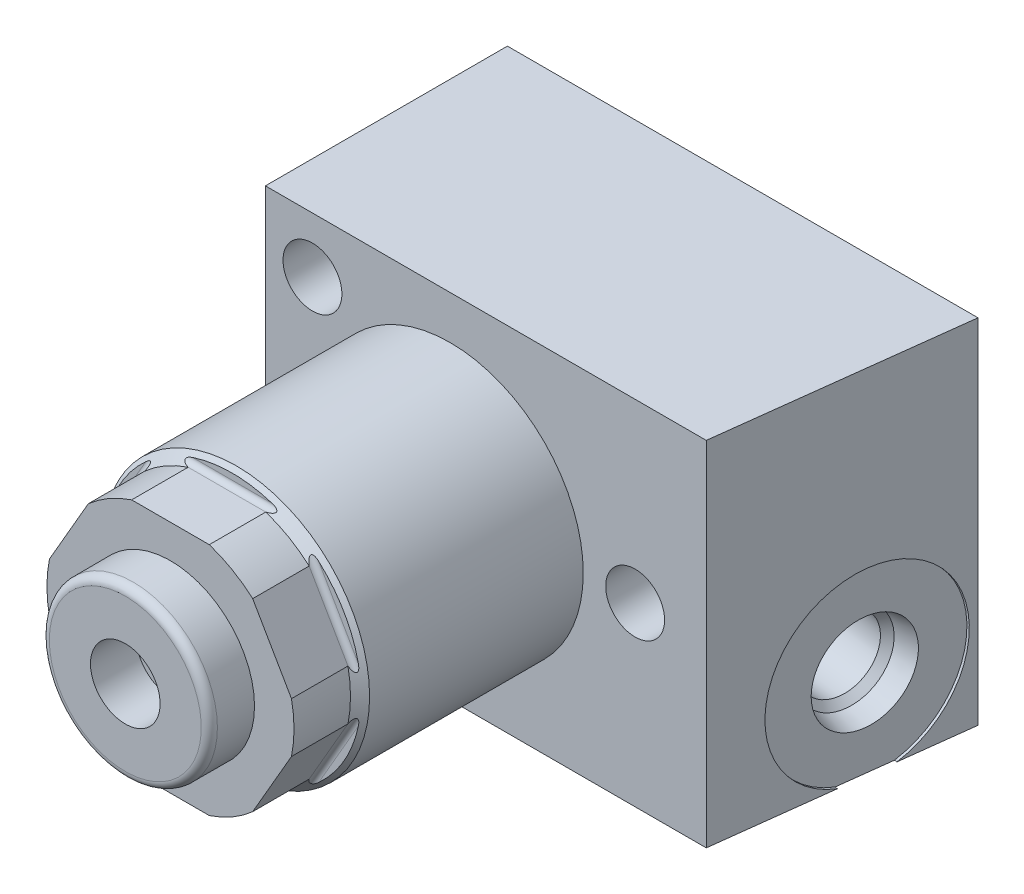
SolidWorks part; units mm, degrees
material "Alloy Steel"
ref_plane "Front Plane" through (0, 0, 0) normal (0, 0, 1) x (1, 0, 0)
ref_plane "Top Plane" through (0, 0, 0) normal (0, 1, 0) x (1, 0, 0)
ref_plane "Right Plane" through (0, 0, 0) normal (1, 0, 0) x (0, 0, -1)
ref_plane "Plane1" through (0, 0, 0) normal (0, 0, 1) x (1, 0, 0)
sketch "Sketch1" plane through (0, 0, 0) normal (0, 0, 1) x (1, 0, 0)
  circle A0 centre (0, 0) radius 12.573
  dimension "D1" = 25.146
extrude "Extrude1" add sketch "Sketch1" along normal blind 40.005
ref_plane "Plane2" through (0, 0, 0) normal (1, 0, 0) x (0, 0, 1)
sketch "Sketch2" plane through (0, 0, 0) normal (1, 0, 0) x (0, 0, 1)
  line L0 (34.163, 12.573) -> (34.163, 11.5887)
  line L1 (34.671, 11.0808) -> (40.005, 11.0808)
  line L2 (33.8709, 0) -> (40.2971, 0) construction
  line L3 (34.163, 12.573) -> (40.005, 12.573)
  line L4 (40.005, 12.573) -> (40.005, 11.0808)
  arc A0 (34.163, 11.5887) -> (34.671, 11.0808) centre (34.671, 11.5887) ccw
  dimension "D1" = 0.508
  dimension "D2" = 5.842
  dimension "D3" = 22.1615
extrude "Cut-Extrude1" cut sketch "Sketch2" against normal mid plane 30.1752
ref_plane "Plane12" through (0, 0, 0) normal (1, 0, 0) x (0, 0, -1)
sketch "Sketch10" plane through (0, 0, 0) normal (1, 0, 0) x (0, 0, -1)
  line L0 (-40.005, 11.6713) -> (-34.671, 11.6713)
  line L1 (-34.671, 11.6713) -> (-33.7693, 12.573)
  line L2 (-33.7693, 12.573) -> (-40.005, 12.573)
  line L3 (-40.005, 12.573) -> (-40.005, 11.6713)
  line L4 (-40.3168, 0) -> (-33.4575, 0) construction
  line L5 (-40.005, 12.573) -> (-40.005, -11.0808) construction
  line L6 (0, 12.573) -> (-40.005, 12.573) construction
  dimension "D1" = 5.334
  dimension "D2" = 45
  dimension "D3" = 23.3426
revolve "Cut-Revolve1" cut sketch "Sketch10" angle 360 about L4
ref_plane "Plane13" through (0, 0, 0) normal (1, 0, 0) x (0, 0, -1)
sketch "Sketch11" plane through (0, 0, 0) normal (1, 0, 0) x (0, 0, -1)
  line L0 (-40.005, 0) -> (-44.2722, 0)
  line L1 (-44.2722, 0) -> (-44.2722, 7.9375)
  line L2 (-44.2722, 7.9375) -> (-40.005, 7.9375)
  line L3 (-40.005, 7.9375) -> (-40.005, 0)
  line L4 (-44.4856, 0) -> (-24.4858, 0) construction
  line L5 (-40.005, 11.6713) -> (-40.005, -11.0808) construction
  dimension "D1" = 15.875
  dimension "D2" = 4.2672
revolve "Revolve1" add sketch "Sketch11" angle 360 about L4
ref_plane "Plane14" through (-3.2893, 0, 44.2722) normal (0, 1, 0) x (-1, 0, 0)
sketch "S2D0011" plane through (-3.2893, 0, 44.2722) normal (0, 1, 0) x (-1, 0, 0)
  line L0 (0, 0) -> (0, -4.318)
  line L1 (0, -4.318) -> (-3.2893, -4.318)
  line L2 (0, 0) -> (-3.2893, 0)
  line L3 (-3.2893, 0) -> (-3.2893, -4.318)
  line L4 (-3.2893, -15.4161) -> (-3.2893, 0.2159) construction
  line L5 (4.6482, 0) -> (-11.2268, 0) construction
  dimension "D1" = 6.5786
  dimension "D2" = 4.318
revolve "Cut-Revolve2" cut sketch "S2D0011" angle 360 about L4
fillet "Fillet1" radius 0.762 1 edges at (7.9375, 0, 44.2722)
ref_plane "Plane15" through (0, 0, 0) normal (0, 1, 0) x (-1, 0, 0)
sketch "Sketch13" plane through (0, 0, 0) normal (0, 1, 0) x (-1, 0, 0)
  line L0 (-27.0002, -9.271) -> (17.4498, -9.271)
  line L1 (17.4498, -9.271) -> (17.4498, 13.589)
  line L2 (17.4498, 13.589) -> (-24.1933, 13.589)
  line L3 (-24.1933, 13.589) -> (-27.0002, -9.271)
  line L4 (-12.573, 0) -> (12.573, 0) construction
  dimension "D1" = 9.271
  dimension "D2" = 17.4498
  dimension "D3" = 22.86
  dimension "D4" = 44.45
  dimension "D5" = 83
extrude "Extrude2" add sketch "Sketch13" along normal blind 16.6687 and the other way blind 16.6687
sketch "Sketch14" plane through (25.4778, 0, 3.1283) normal (0.9925, 0, 0.1219) x (0.1219, 0, -0.9925)
  circle A0 centre (3.0944, -8.382) radius 8.6614
extrude "Cut-Extrude9" cut sketch "Sketch14" against normal blind 0.254
ref_plane "Plane16" through (25.6028, -8.382, 0.026) normal (0, 1, 0) x (-0.1219, 0, 0.9925)
sketch "S2D0002" plane through (25.6028, -8.382, 0.026) normal (0, 1, 0) x (-0.1219, 0, 0.9925)
  line L0 (0, 0) -> (4.5466, 0)
  line L1 (4.5466, 0) -> (4.1066, -2.0701)
  line L2 (4.1066, -2.0701) -> (3.4544, -2.7223)
  line L3 (3.4544, -2.7223) -> (3.4544, -12.192)
  line L4 (3.4544, -12.192) -> (0, -12.192)
  line L5 (0, -12.192) -> (0, 0)
  line L6 (0, -12.8016) -> (0, 0.6096) construction
  dimension "D1" = 12.192
revolve "Cut-Revolve3" cut sketch "S2D0002" angle 360 about L6
ref_plane "Plane17" through (17.4752, 9.7218, -8.345) normal (0, 1, 0) x (-1, 0, 0)
sketch "Sketch16" plane through (17.4752, 9.7218, -8.345) normal (0, 1, 0) x (-1, 0, 0)
  line L0 (0, -0.926) -> (6.35, -0.926)
  line L1 (6.35, -0.926) -> (6.35, 1.487)
  line L2 (6.35, 1.487) -> (2.3876, 1.487)
  line L3 (2.3876, 1.487) -> (2.3876, 11.012)
  line L4 (2.3876, 11.012) -> (0, 12.4467)
  line L5 (0, 12.4467) -> (0, -0.926)
  line L6 (0, -1.5946) -> (0, 13.1153) construction
revolve "Cut-Revolve4" cut sketch "Sketch16" angle 360 about L6
ref_plane "Plane18" through (17.4752, 9.7218, -8.345) normal (0, 1, 0) x (-1, 0, 0)
sketch "Sketch17" plane through (17.4752, 9.7218, -8.345) normal (0, 1, 0) x (-1, 0, 0)
  line L0 (0, -1.0466) -> (0, 1.6077) construction
  circle A0 centre (-5.1435, 0.2805) radius 1.2065
revolve "Revolve2" add sketch "Sketch17" angle 360 about L0
pattern_circular "CirPattern2" count 6 over 360 about axis through (0, 0, 0) along (0, 0, 1) of "Cut-Extrude1"
hole_wizard "Hole1" positions "Sketch19" profile "Sketch18" legacy end condition up to next
sketch "Sketch19" plane through (0, 0, 13.589) normal (0, 0, 1) x (1, 0, 0)
  line L0 (0, 0) -> (-19.5254, 0) construction
  point P0 (-13.0048, -11.43)
  point P6 (17.4752, 0)
  point P10 (-13.0048, 11.43)
  dimension "D1" = 17.4752
  dimension "D2" = 22.86
  dimension "D3" = 13.0048
sketch "Sketch18" plane through (-13.0048, -11.43, 13.589) normal (1, 0, 0) x (0, -1, 0)
  line L0 (0, 0) -> (0, 22.86)
  line L1 (0, 22.86) -> (2.7813, 22.86)
  line L2 (2.7813, 22.86) -> (2.7813, 0)
  line L3 (2.7813, 0) -> (0, 0)
  line L4 (0, 110) -> (0, -10) construction
  dimension "Diameter" = 5.5626
  dimension "Depth" = 22.86
